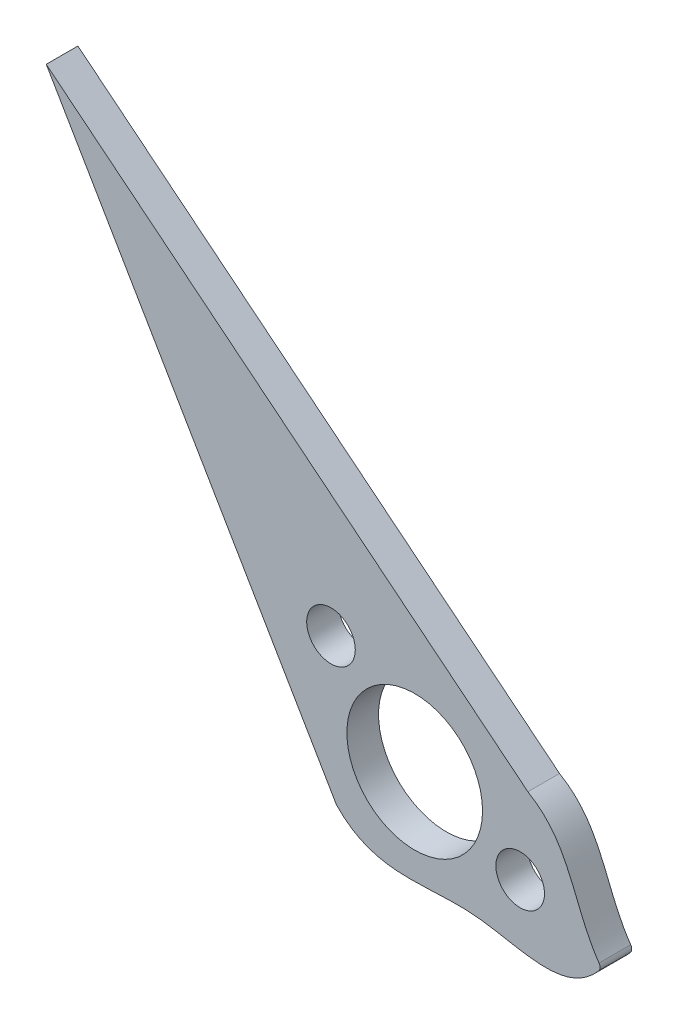
SolidWorks part; units mm, degrees
material "Titanium Ti-5Al-2.5Sn"
ref_plane "Front Plane" through (0, 0, 0) normal (0, 0, 1) x (1, 0, 0)
ref_plane "Top Plane" through (0, 0, 0) normal (0, 1, 0) x (1, 0, 0)
ref_plane "Right Plane" through (0, 0, 0) normal (1, 0, 0) x (0, 0, -1)
sketch "Sketch1" plane through (0, 0, 0) normal (0, 0, 1) x (1, 0, 0)
  line L0 (-6.9149, -6.0039) -> (-32.5978, 37.9129)
  line L1 (-32.5978, 37.9129) -> (10.0126, 3.4802)
  circle A1 centre (0, 0) radius 6
  circle A4 centre (-7.4069, 6.7184) radius 2.15
  circle A5 centre (9.3292, -3.6008) radius 2.15
  spline S0 degree 3 poles (10.0126, 3.4802) (13.9762, 1.1927) (14.0145, -3.519) (16.535, -6.7957) knots 0 0 0 0 1 1 1 1
  spline S1 degree 3 poles (-6.9149, -6.0039) (-3.4527, -9.6103) (5.0341, -6.4625) (13.4161, -10.7833) (16.535, -6.7957) knots 0 0 0 0 0.51712 1 1 1 1
  point P1 (-2.2278, -8.5444)
  point P8 (15.3546, -5.3741)
  point P11 (17.2843, -7.2968)
  point P13 (15.4783, -5.1069)
  point P14 (13.2728, -0.1385)
  point P15 (0, 0)
  point P19 (12.44, -9.1618)
  point P23 (16.535, -6.7957)
  dimension "D1" = 12
  dimension "D2" = 50
  dimension "D3" = 10
  dimension "D5" = 9
  dimension "D4" = 10
  dimension "D6" = 9
extrude "Boss-Extrude3" add sketch "Sketch1" along normal blind 2.8
fillet "Fillet2" radius 0.5 1 edges at (16.535, -6.7957, 1.4)
